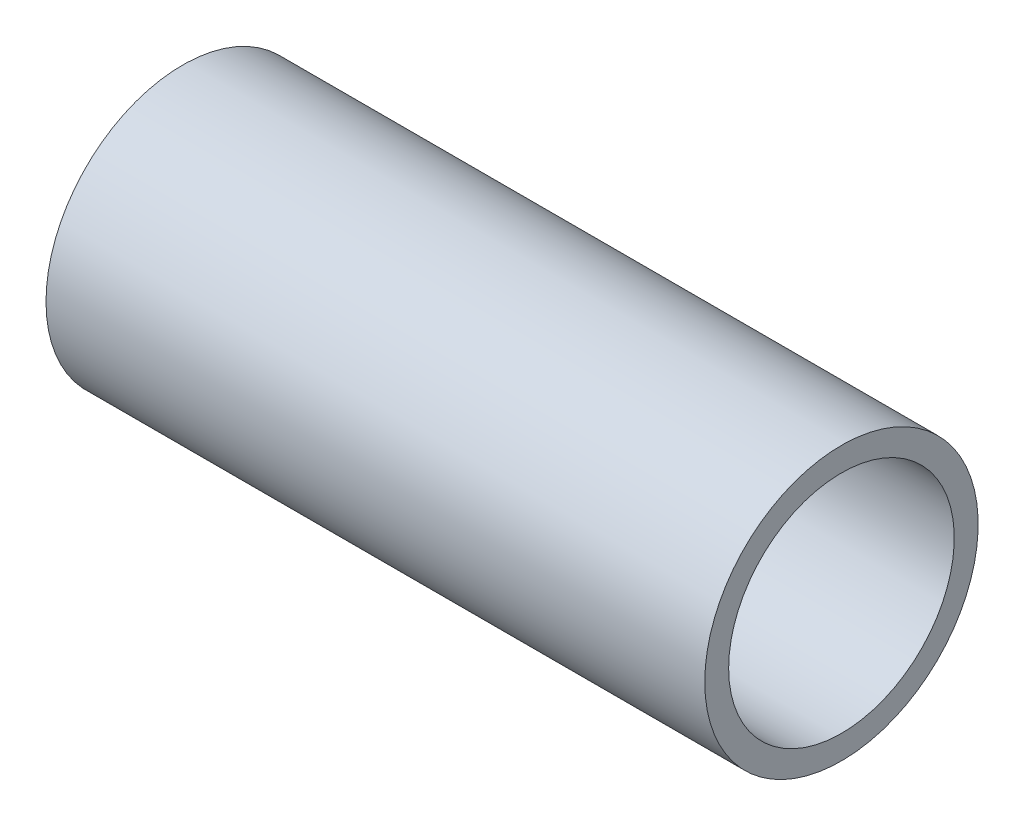
SolidWorks part; units mm, degrees
ref_plane "Front Plane" through (0, 0, 0) normal (0, 0, 1) x (1, 0, 0)
ref_plane "Top Plane" through (0, 0, 0) normal (0, 1, 0) x (1, 0, 0)
ref_plane "Right Plane" through (0, 0, 0) normal (1, 0, 0) x (0, 0, -1)
sketch "Sketch1" plane through (0, 0, 0) normal (0, 0, 1) x (1, 0, 0)
  line L0 (0, 26.0634) -> (0, -23.9285) construction
  line L1 (-19.5698, 0) -> (54.9733, 0) construction
  line L3 (0, 21.082) -> (101.6, 21.082)
  line L4 (0, 21.082) -> (0, 17.399)
  line L5 (0, 17.399) -> (101.6, 17.399)
  line L6 (101.6, 21.082) -> (101.6, 17.399)
  dimension "D1" = 42.164
  dimension "D2" = 34.798
  dimension "D3" = 101.6
revolve "Revolve1" add sketch "Sketch1" angle 360 about L1
